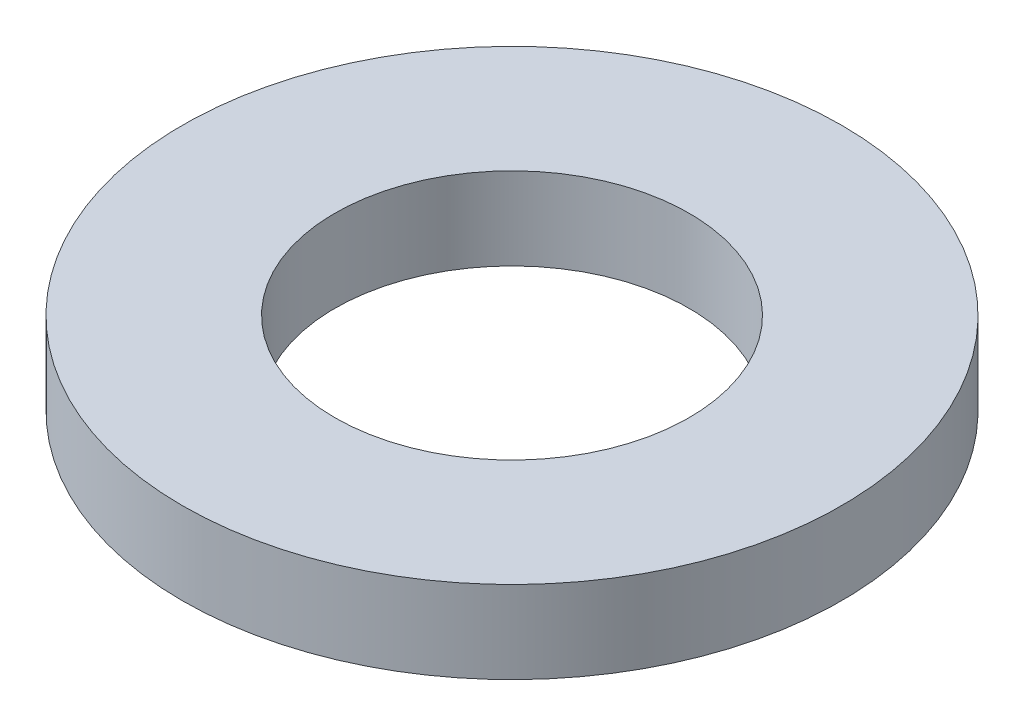
SolidWorks part; units mm, degrees
ref_plane "Front Plane" through (0, 0, 0) normal (0, 0, 1) x (1, 0, 0)
ref_plane "Top Plane" through (0, 0, 0) normal (0, 1, 0) x (1, 0, 0)
ref_plane "Right Plane" through (0, 0, 0) normal (1, 0, 0) x (0, 0, -1)
sketch "Sketch1" plane through (0, 0, 0) normal (0, 1, 0) x (1, 0, 0)
  circle A0 centre (0, 0) radius 2.15
  circle A1 centre (0, 0) radius 4
  dimension "D1" = 4.3
  dimension "D2" = 8
extrude "Boss-Extrude1" add sketch "Sketch1" along normal blind 1
